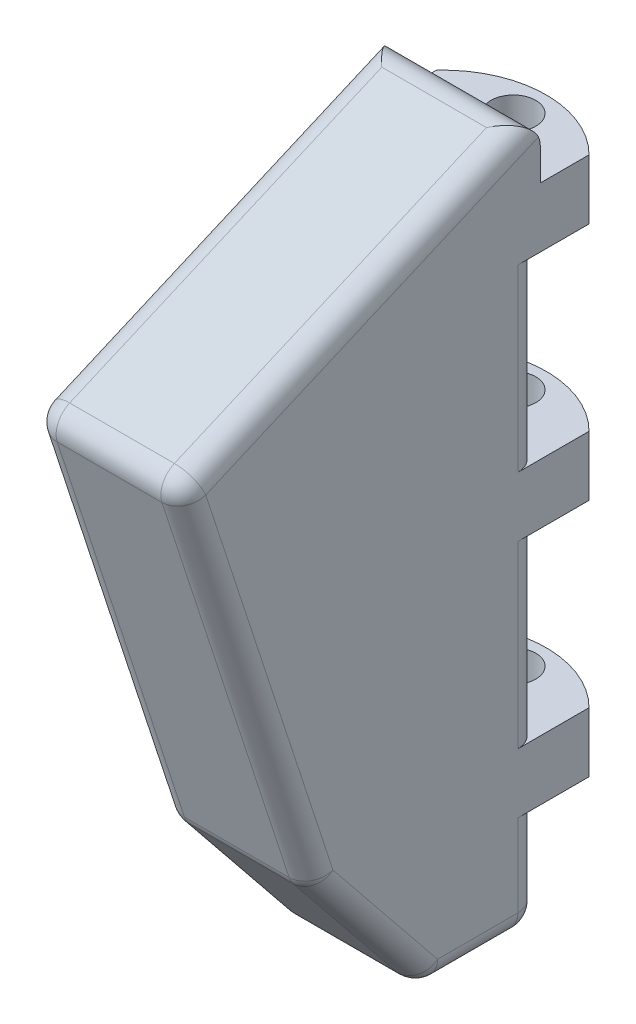
SolidWorks part; units mm, degrees
ref_plane "Front Plane" through (0, 0, 0) normal (0, 0, 1) x (1, 0, 0)
ref_plane "Top Plane" through (0, 0, 0) normal (0, 1, 0) x (1, 0, 0)
ref_plane "Right Plane" through (0, 0, 0) normal (1, 0, 0) x (0, 0, -1)
sketch "Sketch1" plane through (0, 0, 0) normal (0, 0, 1) x (1, 0, 0)
  line L1 (0, 0) -> (10, 0)
  line L2 (0, 0) -> (0, -50)
  line L3 (0, -50) -> (10, -50)
  line L4 (10, 0) -> (10, -50)
  dimension "D1" = 10
  dimension "D2" = 50
extrude "Boss-Extrude1" add sketch "Sketch1" along normal blind 40
sketch "Sketch2" plane through (10, 0, 0) normal (1, 0, 0) x (0, 0, -1)
  line L0 (0, 0) -> (-40, -17.2778)
  line L2 (-40, -17.2778) -> (-13.5839, -50)
  line L3 (-40, -50) -> (0, -50) construction
  line L4 (-13.5839, -50) -> (0, -50)
  line L5 (0, -50) -> (0, 0)
  line L6 (0, 0) -> (-40, 0)
  line L7 (-40, 0) -> (-40, -50)
  line L8 (-40, -50) -> (-13.5839, -50)
  line L9 (-27.4298, -11.8481) -> (-23.7903, -37.357)
  line M6 (0, 0) -> (-40, 0)
  line M7 (-40, 0) -> (-40, -50)
  line M8 (-40, -50) -> (0, -50)
extrude "Cut-Extrude1" cut sketch "Sketch2" against normal blind 40 contours L0 M6 M7 | L2 M7 M8
sketch "Sketch3" plane through (10, 0, 0) normal (1, 0, 0) x (0, 0, -1)
  line L0 (-30.2113, -13.0496) -> (-21.1962, -40.5705)
  line L1 (0, 0) -> (-40, -17.2778) construction
  line L2 (-40, -17.2778) -> (-13.5839, -50) construction
  line L3 (-30.2113, -13.0496) -> (-40, -17.2778)
  line L4 (-40, -17.2778) -> (-21.1962, -40.5705)
extrude "Cut-Extrude2" cut sketch "Sketch3" against normal blind 40
sketch "Sketch4" plane through (0, 0, 0) normal (0, 0, -1) x (-1, 0, 0)
  line L0 (0, 0) -> (0, -50) construction
  line L1 (-10, 0) -> (0, 0)
  line L2 (-10, 0) -> (-10, -7)
  line L3 (-10, -7) -> (0, -7)
  line L4 (0, 0) -> (0, -7)
  line L5 (-10, -50) -> (-10, 0) construction
  line L6 (-10, -11) -> (0, -11)
  line L7 (-10, -11) -> (-10, -23)
  line L8 (-10, -23) -> (0, -23)
  line L9 (0, -11) -> (0, -23)
  line L10 (0, -50) -> (-10, -50) construction
  line L11 (-10, -27) -> (0, -27)
  line L12 (-10, -27) -> (-10, -39)
  line L13 (-10, -39) -> (0, -39)
  line L14 (0, -27) -> (0, -39)
  line L15 (-10, -43) -> (0, -43)
  line L16 (-10, -43) -> (-10, -50)
  line L17 (-10, -50) -> (0, -50)
  line L18 (0, -43) -> (0, -50)
  dimension "D1" = 7
  dimension "D2" = 12
  dimension "D3" = 4
  dimension "D4" = 4
  dimension "D5" = 4
  dimension "D6" = 7
  dimension "D7" = 12
extrude "Cut-Extrude3" cut sketch "Sketch4" against normal blind 6
sketch "Sketch5" plane through (0, -43, 0) normal (0, -1, 0) x (1, 0, 0)
  circle A0 centre (5.0659, 2.8678) radius 1.5
  dimension "D1" = 3
extrude "Cut-Extrude4" cut sketch "Sketch5" against normal blind 38
sketch "Sketch6" plane through (0, -43, 0) normal (0, -1, 0) x (1, 0, 0)
  line L2 (0, 2.9419) -> (0, 6)
  line L3 (0, 6) -> (10, 6)
  line L4 (10, 6) -> (10, 2.7419)
  line L5 (10, 6) -> (10, 0) construction
  line L6 (0, 2.9419) -> (0, 0)
  line L7 (0, 0) -> (10, 0)
  line L8 (10, 0) -> (10, 2.7419)
  arc A0 (0, 2.9419) -> (10, 2.7419) centre (5.0953, 7.6094) ccw
  line M2 (0, 0) -> (10, 0)
  line M3 (10, 0) -> (10, 6)
  line M5 (0, 6) -> (0, 0)
extrude "Cut-Extrude5" cut sketch "Sketch6" against normal blind 38 contours A0 M5 M2 M3
fillet "Fillet1" radius 1.5 19 edges at (0, -7.8206, 18.1056) (5, -2.5917, 6) (10, -7.8206, 18.1056) (0, -50, 9.7919) (10, -50, 9.7919) (5, -50, 6) (10, -45.2852, 17.39) (5, -50, 13.5839) (0, -45.2852, 17.39) (0, -26.81, 25.7037) (5, -13.0496, 30.2113) (10, -26.81, 25.7037) (5, -40.5705, 21.1962) (0, -46.5, 6) (0, -33, 6) (0, -17, 6) (10, -46.5, 6) (10, -33, 6) (10, -17, 6)
